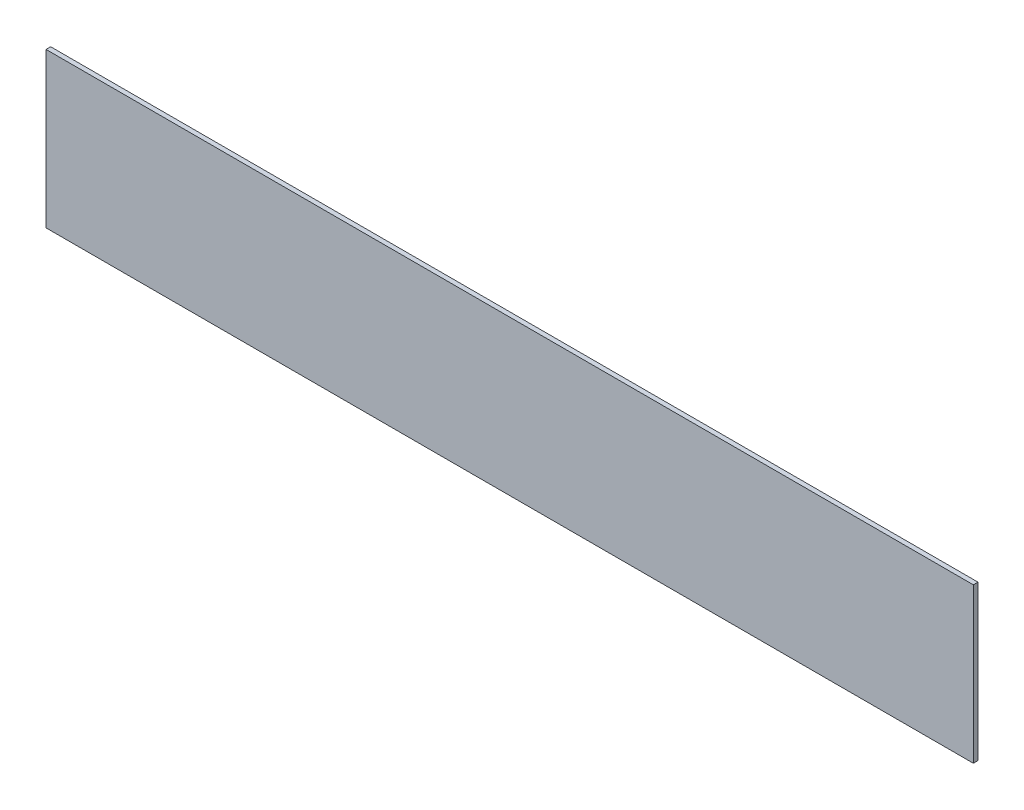
SolidWorks part; units mm, degrees
material "PMMA"
ref_plane "Front Plane" through (0, 0, 0) normal (0, 0, 1) x (1, 0, 0)
ref_plane "Top Plane" through (0, 0, 0) normal (0, 1, 0) x (1, 0, 0)
ref_plane "Right Plane" through (0, 0, 0) normal (1, 0, 0) x (0, 0, -1)
sketch "Sketch2" plane through (0, 0, 0) normal (0, 0, 1) x (1, 0, 0)
  line L1 (0, 0) -> (600, 0)
  line L2 (0, 0) -> (0, 100)
  line L3 (0, 100) -> (600, 100)
  line L4 (600, 0) -> (600, 100)
  dimension "D1" = 600
  dimension "D2" = 100
extrude "Boss-Extrude1" add sketch "Sketch2" along normal blind 3
